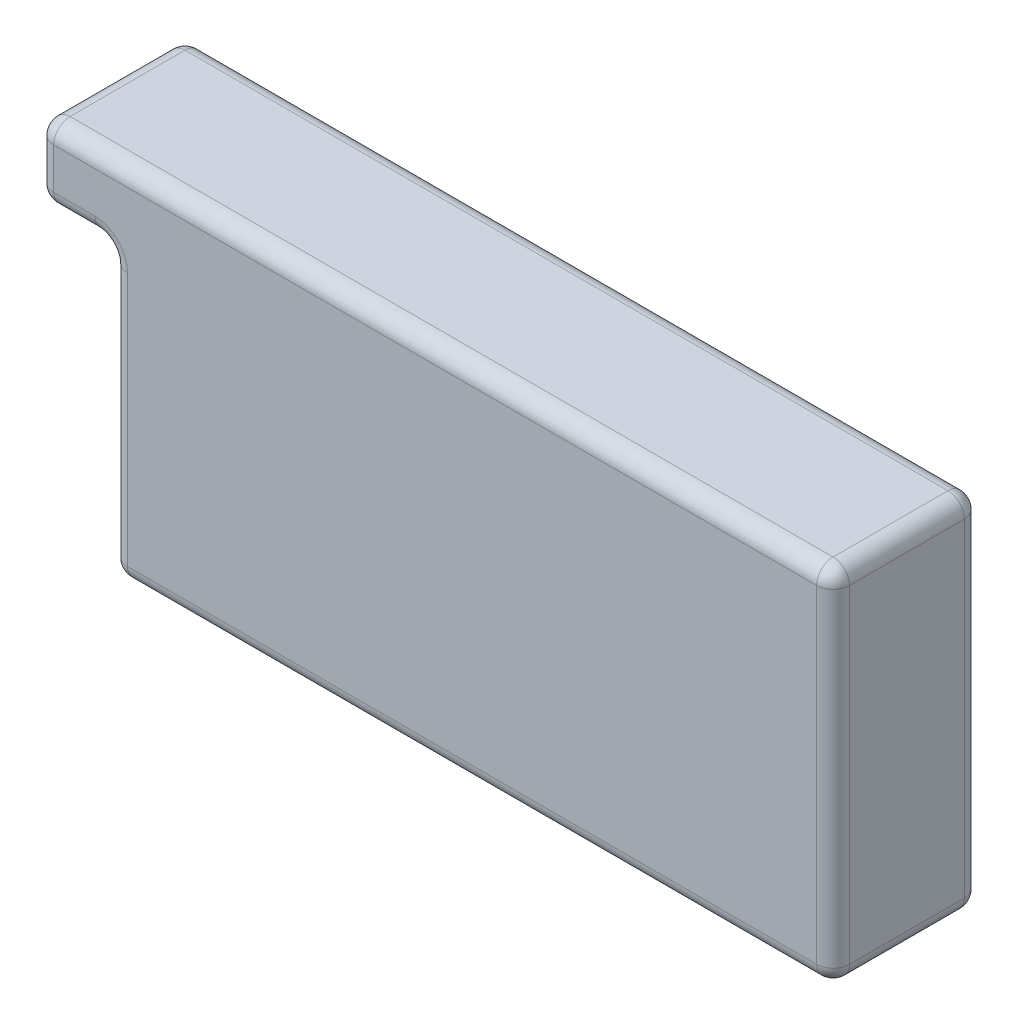
SolidWorks part; units mm, degrees
ref_plane "Plan de face" through (0, 0, 0) normal (0, 0, 1) x (1, 0, 0)
ref_plane "Plan de dessus" through (0, 0, 0) normal (0, 1, 0) x (1, 0, 0)
ref_plane "Plan de droite" through (0, 0, 0) normal (1, 0, 0) x (0, 0, -1)
sketch "Esquisse1" plane through (0, 0, 0) normal (0, 0, 1) x (1, 0, 0)
  line L1 (0, 0) -> (44, 0)
  line L2 (0, 0) -> (0, -22)
  line L3 (0, -22) -> (44, -22)
  line L4 (44, 0) -> (44, -22)
  dimension "D1" = 22
  dimension "D2" = 44
extrude "Boss.-Extru.1" add sketch "Esquisse1" along normal blind 9
sketch "Esquisse2" plane through (0, 0, 0) normal (-1, 0, 0) x (0, 0, 1)
  line L1 (9, -4.5) -> (0, -4.5)
  line L2 (9, -4.5) -> (9, 0)
  line L3 (9, 0) -> (0, 0)
  line L4 (0, -4.5) -> (0, 0)
  dimension "D1" = 4.5
  dimension "D2" = 9
extrude "Boss.-Extru.2" add sketch "Esquisse2" along normal blind 4.5 and the other way blind 9
fillet "Congé2" radius 1 18 edges at (-4.5, -4.5, 4.5) (44, -22, 4.5) (44, 0, 4.5) (-4.5, 0, 4.5) (22, -22, 0) (44, -11, 0) (19.75, 0, 0) (-4.5, -2.25, 0) (-2.25, -4.5, 0) (0, -22, 4.5) (0, -13.25, 0) (0, -4.5, 4.5) (44, -11, 9) (22, -22, 9) (0, -13.25, 9) (-2.25, -4.5, 9) (-4.5, -2.25, 9) (19.75, 0, 9)
